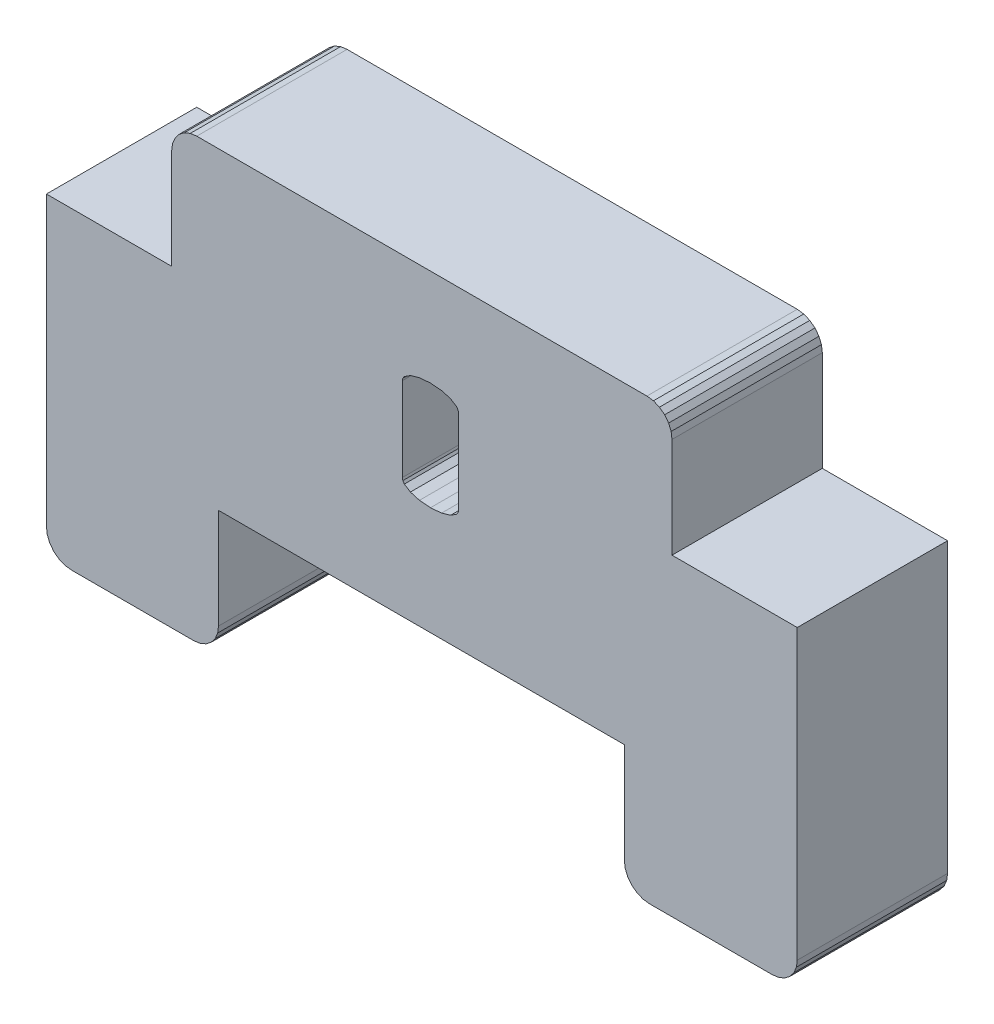
SolidWorks part; units mm, degrees
material "Maple"
ref_plane "Front Plane" through (0, 0, 0) normal (0, 0, 1) x (1, 0, 0)
ref_plane "Top Plane" through (0, 0, 0) normal (0, 1, 0) x (1, 0, 0)
ref_plane "Right Plane" through (0, 0, 0) normal (1, 0, 0) x (0, 0, -1)
sketch "Sketch1" plane through (0, 0, 0) normal (0, 0, 1) x (1, 0, 0)
  line L415 (-438.9982, -234.7022) -> (-439.0323, -234.4433)
  line L416 (-438.9982, -234.7022) -> (-438.9982, -238.7022)
  line L417 (-438.9982, -238.7022) -> (-433.9982, -238.7022)
  line L418 (-434.1322, -250.7022) -> (-434.2911, -250.9093)
  line L419 (-434.2911, -250.9093) -> (-434.4982, -251.0682)
  line L420 (-434.4982, -251.0682) -> (-434.7394, -251.1681)
  line L421 (-434.7394, -251.1681) -> (-434.9982, -251.2022)
  line L422 (-439.8982, -251.2022) -> (-434.9982, -251.2022)
  line L423 (-440.1571, -251.1681) -> (-440.3982, -251.0682)
  line L424 (-458.8327, -234.2022) -> (-458.6738, -233.995)
  line L425 (-458.9326, -234.4433) -> (-458.8327, -234.2022)
  line L426 (-463.2255, -251.1681) -> (-463.4667, -251.0682)
  line L427 (-463.8327, -250.7022) -> (-463.9326, -250.461)
  line L428 (-439.8982, -251.2022) -> (-440.1571, -251.1681)
  line L429 (-439.7394, -233.7362) -> (-439.9982, -233.7022)
  line L430 (-433.9982, -250.2022) -> (-433.9982, -238.7022)
  line L431 (-463.6738, -250.9093) -> (-463.8327, -250.7022)
  line L432 (-463.4667, -251.0682) -> (-463.6738, -250.9093)
  line L433 (-458.9667, -234.7022) -> (-458.9326, -234.4433)
  line L434 (-458.4667, -233.8361) -> (-458.2255, -233.7362)
  line L435 (-457.2322, -250.7022) -> (-457.3911, -250.9093)
  line L436 (-457.3911, -250.9093) -> (-457.5982, -251.0682)
  line L437 (-457.5982, -251.0682) -> (-457.8394, -251.1681)
  line L438 (-457.8394, -251.1681) -> (-458.0982, -251.2022)
  line L439 (-462.9667, -251.2022) -> (-458.0982, -251.2022)
  line L440 (-462.9667, -251.2022) -> (-463.2255, -251.1681)
  line L441 (-463.9326, -250.461) -> (-463.9667, -250.2022)
  line L442 (-463.9667, -238.7022) -> (-463.9667, -250.2022)
  line L443 (-463.9667, -238.7022) -> (-458.9667, -238.7022)
  line L444 (-439.0323, -234.4433) -> (-439.1322, -234.2022)
  line L445 (-439.1322, -234.2022) -> (-439.2911, -233.995)
  line L446 (-439.2911, -233.995) -> (-439.4982, -233.8361)
  line L447 (-439.4982, -233.8361) -> (-439.7394, -233.7362)
  line L448 (-457.9667, -233.7022) -> (-439.9982, -233.7022)
  line L449 (-458.2255, -233.7362) -> (-457.9667, -233.7022)
  line L450 (-458.6738, -233.995) -> (-458.4667, -233.8361)
  line L451 (-458.9667, -238.7022) -> (-458.9667, -234.7022)
  line L452 (-457.1323, -250.461) -> (-457.2322, -250.7022)
  line L453 (-457.0982, -250.2022) -> (-457.1323, -250.461)
  line L454 (-457.0982, -250.2022) -> (-457.0982, -246.2022)
  line L455 (-457.0982, -246.2022) -> (-440.8982, -246.2022)
  line L456 (-440.8982, -246.2022) -> (-440.8982, -250.2022)
  line L457 (-440.8642, -250.461) -> (-440.8982, -250.2022)
  line L458 (-440.7643, -250.7022) -> (-440.8642, -250.461)
  line L459 (-440.6053, -250.9093) -> (-440.7643, -250.7022)
  line L460 (-440.3982, -251.0682) -> (-440.6053, -250.9093)
  line L461 (-434.0323, -250.461) -> (-434.1322, -250.7022)
  line L462 (-433.9982, -250.2022) -> (-434.0323, -250.461)
  line L8662 (-449.761, -241.4005) -> (-449.7409, -241.4967)
  line L8663 (-449.7409, -241.4967) -> (-449.6806, -241.5855)
  line L8664 (-449.6806, -241.5855) -> (-449.4394, -241.7408)
  line L8665 (-449.4394, -241.7408) -> (-449.0781, -241.8462)
  line L8666 (-449.0781, -241.8462) -> (-448.6371, -241.8813)
  line L8667 (-448.6371, -241.8813) -> (-448.1961, -241.8462)
  line L8668 (-448.1961, -241.8462) -> (-447.8347, -241.7408)
  line L8669 (-447.8347, -241.7408) -> (-447.5936, -241.5855)
  line L8670 (-447.5936, -241.5855) -> (-447.5333, -241.4967)
  line L8671 (-447.5333, -241.4967) -> (-447.5132, -241.4005)
  line L8672 (-447.5132, -241.4005) -> (-447.5132, -238.0538)
  line L8673 (-447.5132, -238.0538) -> (-447.5333, -237.9576)
  line L8674 (-447.5333, -237.9576) -> (-447.5936, -237.8688)
  line L8675 (-447.5936, -237.8688) -> (-447.8347, -237.7135)
  line L8676 (-447.8347, -237.7135) -> (-448.1961, -237.6081)
  line L8677 (-448.1961, -237.6081) -> (-448.6371, -237.573)
  line L8678 (-448.6371, -237.573) -> (-449.0781, -237.6081)
  line L8679 (-449.0781, -237.6081) -> (-449.4394, -237.7135)
  line L8680 (-449.4394, -237.7135) -> (-449.6806, -237.8688)
  line L8681 (-449.6806, -237.8688) -> (-449.7409, -237.9576)
  line L8682 (-449.7409, -237.9576) -> (-449.761, -238.0538)
  line L8683 (-449.761, -238.0538) -> (-449.761, -241.4005)
  line L8684 (-447.5132, -241.4005) -> (-447.5333, -241.4967)
  line L8685 (-447.5333, -241.4967) -> (-447.5936, -241.5855)
  line L8686 (-447.5936, -241.5855) -> (-447.8347, -241.7408)
  line L8687 (-447.8347, -241.7408) -> (-448.1961, -241.8462)
  line L8688 (-448.1961, -241.8462) -> (-448.6371, -241.8813)
  line L8689 (-448.6371, -241.8813) -> (-449.0781, -241.8462)
  line L8690 (-449.0781, -241.8462) -> (-449.4394, -241.7408)
  line L8691 (-449.4394, -241.7408) -> (-449.6806, -241.5855)
  line L8692 (-449.6806, -241.5855) -> (-449.7409, -241.4967)
  line L8693 (-449.7409, -241.4967) -> (-449.761, -241.4005)
  line L8694 (-449.761, -241.4005) -> (-449.761, -238.0538)
  line L8695 (-449.761, -238.0538) -> (-449.7409, -237.9576)
  line L8696 (-449.7409, -237.9576) -> (-449.6806, -237.8688)
  line L8697 (-449.6806, -237.8688) -> (-449.4394, -237.7135)
  line L8698 (-449.4394, -237.7135) -> (-449.0781, -237.6081)
  line L8699 (-449.0781, -237.6081) -> (-448.6371, -237.573)
  line L8700 (-448.6371, -237.573) -> (-448.1961, -237.6081)
  line L8701 (-448.1961, -237.6081) -> (-447.8347, -237.7135)
  line L8702 (-447.8347, -237.7135) -> (-447.5936, -237.8688)
  line L8703 (-447.5936, -237.8688) -> (-447.5333, -237.9576)
  line L8704 (-447.5333, -237.9576) -> (-447.5132, -238.0538)
  line L8705 (-447.5132, -238.0538) -> (-447.5132, -241.4005)
  line L8706 (-448.481, -241.276) -> (-447.5194, -242.4937)
extrude "Boss-Extrude1" add sketch "Sketch1" along normal blind 6 contours L462 L430 L417 L416 L415 L444 L445 L446 L447 L429 L448 L449 L434 L450 L424 L425 L433 L451 L443 L442 L441 L427 L431 L432 L426 L440 L439 L438 L437 L436 L435 L452 L453 L454 L455 L456 L457 L458 L459 L460 L423 L428 L422 L421 L420 L419 L418 L461 L8683 L8682
